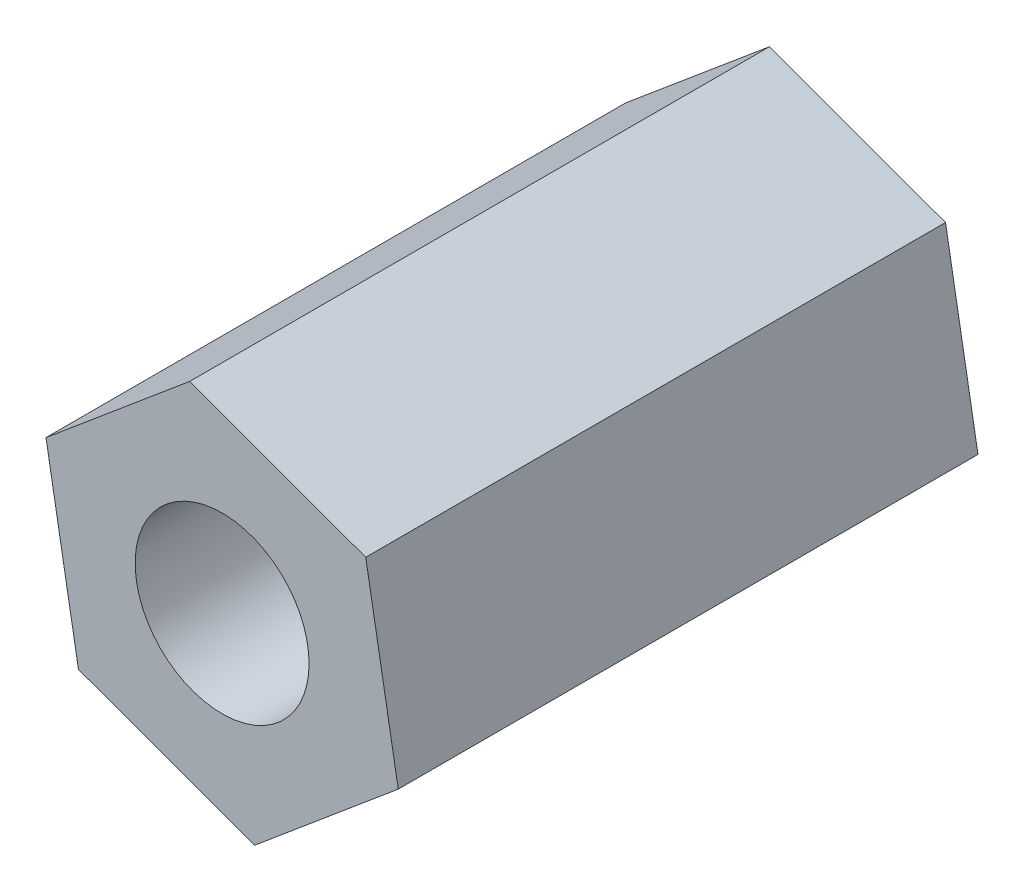
SolidWorks part; units mm, degrees
ref_plane "前视基准面" through (0, 0, 0) normal (0, 0, 1) x (1, 0, 0)
ref_plane "上视基准面" through (0, 0, 0) normal (0, 1, 0) x (1, 0, 0)
ref_plane "右视基准面" through (0, 0, 0) normal (1, 0, 0) x (0, 0, -1)
other "Configuration Table"
sketch "草图1" plane through (0, 0, 0) normal (0, 0, 1) x (1, 0, 0)
  line L1 (-129.7416, -57.0864) -> (-127.2639, -55.0092)
  line L2 (-127.2639, -55.0092) -> (-127.824, -51.825)
  line L3 (-127.824, -51.825) -> (-130.8617, -50.7179)
  line L4 (-130.8617, -50.7179) -> (-133.3394, -52.7951)
  line L5 (-133.3394, -52.7951) -> (-132.7793, -55.9793)
  line L6 (-132.7793, -55.9793) -> (-129.7416, -57.0864)
  circle A0 centre (-130.3017, -53.9021) radius 2.8 construction
  circle A1 centre (-130.3017, -53.9021) radius 1.5
  dimension "D2" = 3
  dimension "D1" = 5.6
extrude "凸台-拉伸1" add sketch "草图1" along normal blind 10
